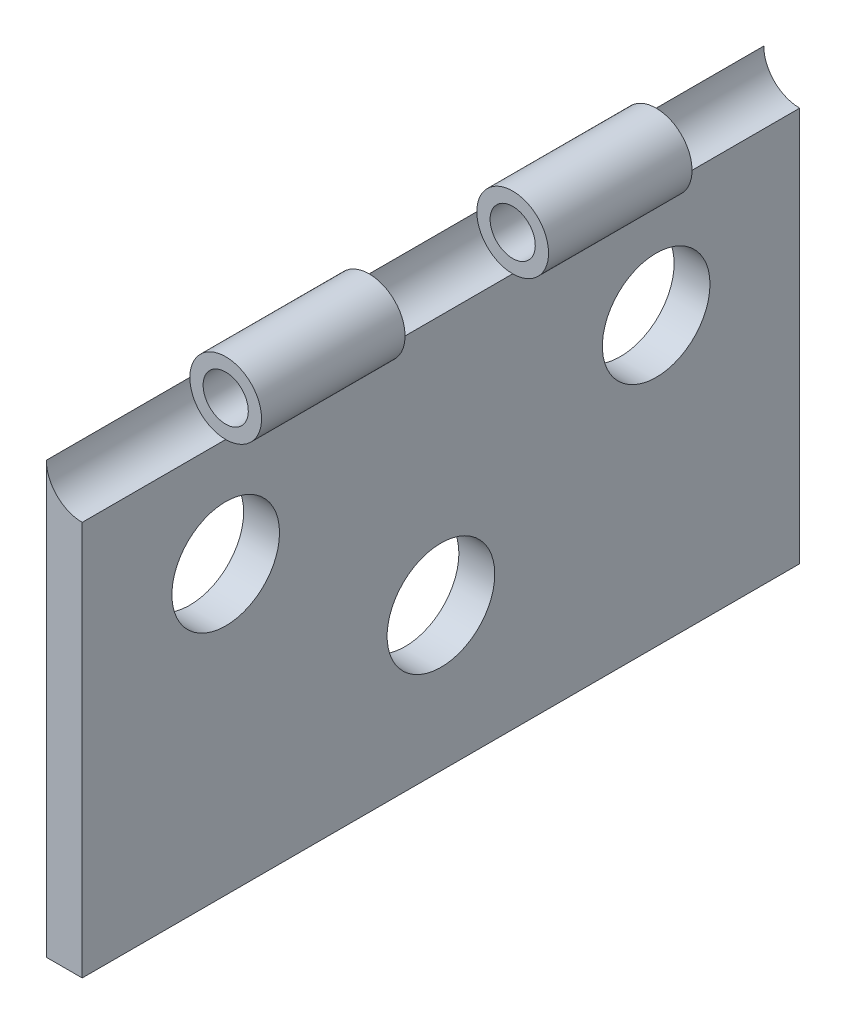
SolidWorks part; units mm, degrees
ref_plane "Front Plane" through (0, 0, 0) normal (0, 0, 1) x (1, 0, 0)
ref_plane "Top Plane" through (0, 0, 0) normal (0, 1, 0) x (1, 0, 0)
ref_plane "Right Plane" through (0, 0, 0) normal (1, 0, 0) x (0, 0, -1)
sketch "Sketch1" plane through (0, 0, 0) normal (1, 0, 0) x (0, 0, -1)
  line L0 (0, 20) -> (50, 20) construction
  line L1 (0, 0) -> (50, 0)
  line L2 (0, 0) -> (0, 30)
  line L3 (0, 30) -> (50, 30)
  line L4 (50, 0) -> (50, 30)
  line L5 (0, 10) -> (50, 10) construction
  circle A0 centre (40, 20) radius 3.75
  circle A1 centre (25, 10) radius 3.75
  circle A2 centre (10, 20) radius 3.75
  dimension "D5" = 7.5
  dimension "D1" = 50
  dimension "D2" = 30
  dimension "D3" = 10
  dimension "D4" = 10
  dimension "D6" = 10
  dimension "D7" = 10
extrude "Boss-Extrude1" add sketch "Sketch1" along normal blind 2.5
ref_plane "Plane1" through (2.5, 30, -50) normal (0, 0, 1) x (1, 0, 0)
sketch "Sketch3" plane through (0, 0, -50) normal (0, 0, -1) x (-1, 0, 0)
  line L0 (-2.5, 0) -> (-2.5, 30) construction
  line L1 (0, 0) -> (0, 30) construction
  circle A0 centre (-2.5, 30) radius 2.5
extrude "Boss-Extrude2" add sketch "Sketch3" along normal blind 10 from offset 20 offset against normal yes
pattern_linear "LPattern1" count 2 spacing 20 along (0, 0, 1) of "Boss-Extrude2"
ref_plane "Plane2" through (2.5, 30, -50) normal (-1, 0, 0) x (0, 0, 1)
sketch "Sketch5" plane through (0, 0, -50) normal (0, 0, -1) x (-1, 0, 0)
  circle A0 centre (-2.5, 30) radius 1.575
  dimension "D1" = 3.15
extrude "Cut-Extrude1" cut sketch "Sketch5" against normal blind 50
sketch "Sketch6" plane through (0, 0, -50) normal (0, 0, -1) x (-1, 0, 0)
  circle A0 centre (-2.5, 30) radius 2.5
  arc A1 (-2.5, 28.425) -> (-0.925, 30) centre (-2.5, 30) ccw construction
  arc A2 (0, 30) -> (-2.5, 27.5) centre (-2.5, 30) ccw construction
extrude "Cut-Extrude2" cut sketch "Sketch6" against normal blind 10
pattern_linear "LPattern2" count 3 spacing 20 along (0, 0, 1) of "Cut-Extrude2"
scale "Escala1" scale about origin uniform scaling yes scale factor 0.5
